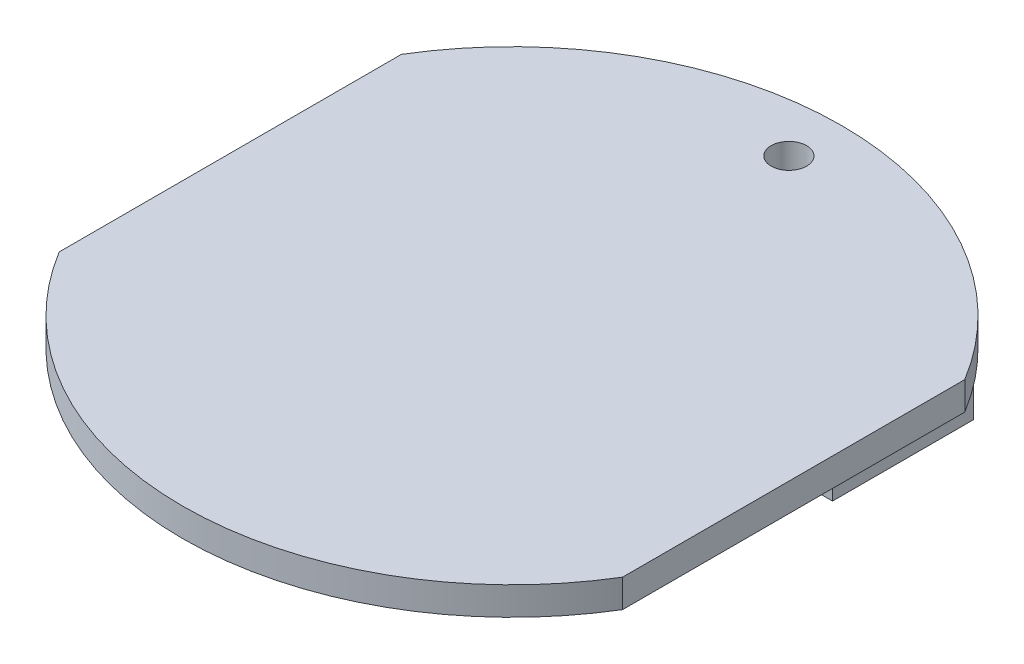
SolidWorks part; units mm, degrees
ref_plane "前视基准面" through (0, 0, 0) normal (0, 0, 1) x (1, 0, 0)
ref_plane "上视基准面" through (0, 0, 0) normal (0, 1, 0) x (1, 0, 0)
ref_plane "右视基准面" through (0, 0, 0) normal (1, 0, 0) x (0, 0, -1)
sketch "草图1" plane through (0, 0, 0) normal (0, 1, 0) x (1, 0, 0)
  circle A0 centre (0, 0) radius 12.5
  dimension "D1" = 25
ref_plane "基准面4" through (0, 11, 0) normal (0, 1, 0) x (1, 0, 0)
sketch "草图2" plane through (0, 11, 0) normal (0, 1, 0) x (1, 0, 0)
  circle A0 centre (0, 0) radius 12
  dimension "D1" = 24
loft "放样1" add profiles "草图2", "草图1"
sketch "草图4" plane through (0, 0, 0) normal (0, 1, 0) x (1, 0, 0)
  line L0 (-1.3523, -2.5) -> (-1.3523, -2.1027)
  line L1 (8, -7.5) -> (-8, -7.5)
  line L2 (8, -7.5) -> (8, -2.5)
  line L3 (8, -2.5) -> (1.3099, -2.5)
  line L4 (-8, -7.5) -> (-8, -2.5)
  line L5 (8, -7.5) -> (-8, -2.5) construction
  line L6 (8, -2.5) -> (-8, -7.5) construction
  line L7 (1.3099, -2.5) -> (1.3099, -2.1293)
  line L8 (-1.3523, -2.5) -> (-8, -2.5)
  arc A0 (1.3099, -2.1293) -> (-1.3523, -2.1027) centre (0, 0) ccw
  point P3 (0, -5)
  dimension "D1" = 5
  dimension "D2" = 16
  dimension "D3" = 5
extrude "切除-拉伸1" cut sketch "草图4" along normal through all contours A0 L0 L8 L4 L1 L2 L3 L7
sketch "草图5" plane through (0, 11, 0) normal (0, 1, 0) x (1, 0, 0)
  line L0 (6.5, 8.991) -> (15.3486, 8.991)
  line L1 (6.5, 2.991) -> (-6.5, 2.991)
  line L2 (6.5, 2.991) -> (6.5, 8.991)
  line L3 (6.5, 8.991) -> (-6.5, 8.991)
  line L4 (-6.5, 2.991) -> (-6.5, 8.991)
  line L5 (6.5, 2.991) -> (-6.5, 8.991) construction
  line L6 (6.5, 8.991) -> (-6.5, 2.991) construction
  line L7 (6.5, 2.991) -> (15.3486, 2.991)
  line L8 (15.3486, 2.991) -> (15.3486, 8.991)
  point P0 (0, 5.991)
  dimension "D1" = 13
  dimension "D2" = 6
extrude "切除-拉伸2" cut sketch "草图5" against normal blind 5
sketch "草图6" plane through (0, 0, 0) normal (1, 0, 0) x (0, 0, -1)
  line L0 (0, 17.1385) -> (0, -6.7643) construction
  line L2 (1.2383, 5.3729) -> (-1.2383, 5.3729)
  line L3 (1.2383, 5.3729) -> (1.2383, 12.2082)
  line L4 (1.2383, 12.2082) -> (-1.2383, 12.2082)
  line L5 (-1.2383, 5.3729) -> (-1.2383, 12.2082)
  line L6 (1.2383, 5.3729) -> (-1.2383, 12.2082) construction
  line L7 (1.2383, 12.2082) -> (-1.2383, 5.3729) construction
  point P3 (0, 8.7905)
extrude "切除-拉伸3" cut sketch "草图6" against normal mid plane 40
sketch "草图7" plane through (0, 11, 0) normal (0, 1, 0) x (1, 0, 0)
  line L0 (-5.9982, 2.991) -> (-5.9982, -3.9694)
  line L1 (11.6213, 2.991) -> (-6.5, 2.991) construction
  line L2 (-5.9982, -3.9694) -> (-8, -3.9694)
  line L3 (-8, -2.5) -> (-8, -7.5) construction
  line L4 (-8, -3.9694) -> (-9.4694, -2.5)
  line L5 (-9.4694, -2.5) -> (-9.4694, 3.9106)
  line L6 (-9.4694, 3.9106) -> (-7.6456, 5.7344)
  line L7 (-7.6456, 5.7344) -> (-6.5, 5.7344)
  line L8 (-6.5, 2.991) -> (-6.5, 8.991) construction
  line L9 (-6.5, 5.7344) -> (-5.9982, 2.991)
extrude "切除-拉伸4" cut sketch "草图7" against normal up to surface (5 mm away) up to face at (1.8949, 6, -6.0561)
sketch "草图9" plane through (0, 11, 0) normal (0, 1, 0) x (1, 0, 0)
  line L0 (-10, 6.0737) -> (-10, -6.0737)
  line L1 (10, 6.0737) -> (10, -6.0737)
  line L2 (-17.5241, 0) -> (23.2871, 0) construction
  arc A2 (-10, -6.0737) -> (10, -6.0737) centre (0, 0) ccw
  arc A3 (10, 6.0737) -> (-10, 6.0737) centre (0, 0) ccw
  circle A4 centre (0, 9.83) radius 0.6309
  point P1 (0, 10.0571)
  point P5 (0, -9.6853)
  point P11 (0, -9.6853)
  point P13 (0, 10.0571)
  dimension "D2" = 10
extrude "凸台-拉伸1" add sketch "草图9" along normal blind 1
sketch "草图11" plane through (0, 0, 0) normal (1, 0, 0) x (0, 0, -1)
  line L0 (11.0001, 11) -> (-11.0001, 11) construction
  line L1 (13.6323, 11) -> (-13.814, 11)
  line L2 (13.6323, 11) -> (13.6323, -0.7934)
  line L3 (13.6323, -0.7934) -> (-13.814, -0.7934)
  line L4 (-13.814, 11) -> (-13.814, -0.7934)
extrude "切除-拉伸5" cut sketch "草图11" against normal mid plane 43.5
sketch "草图10" plane through (0, 11, 0) normal (0, -1, 0) x (1, 0, 0)
  line L1 (7.889, -8.491) -> (3.9975, -8.491)
  line L2 (7.889, -8.491) -> (7.889, -3.491)
  line L3 (7.889, -3.491) -> (3.9975, -3.491)
  line L4 (3.9975, -8.491) -> (3.9975, -3.491)
extrude "凸台-拉伸2" add sketch "草图10" along normal blind 2.5
